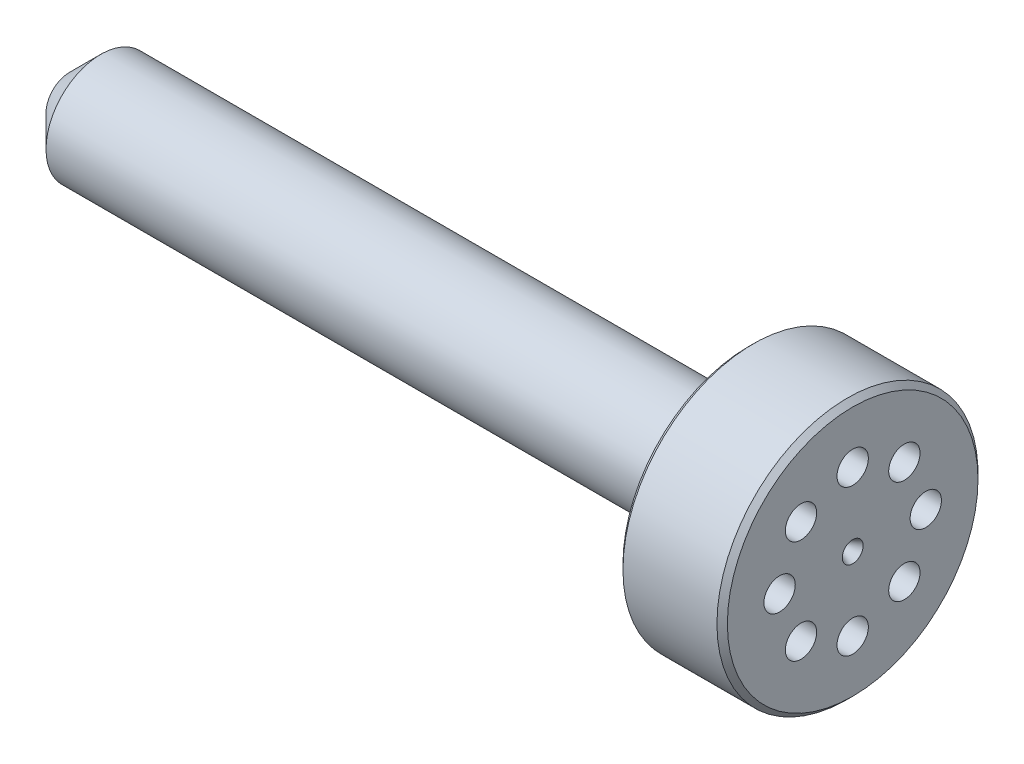
SolidWorks part; units mm, degrees
ref_plane "Front Plane" through (0, 0, 0) normal (0, 0, 1) x (1, 0, 0)
ref_plane "Top Plane" through (0, 0, 0) normal (0, 1, 0) x (1, 0, 0)
ref_plane "Right Plane" through (0, 0, 0) normal (1, 0, 0) x (0, 0, -1)
sketch "Sketch2" plane through (0, 0, 0) normal (0, 1, 0) x (1, 0, 0)
  line L0 (0, 0) -> (0, 17938.5923) construction
  line L1 (0, 0) -> (-17938.5923, 0) construction
  line L2 (-34, 1) -> (-34, 2.25)
  line L3 (-31, 5.25) -> (31, 5.25)
  line L4 (31, 5.25) -> (31, 12.5)
  line L5 (31, 12.5) -> (41, 12.5)
  line L6 (41, 12.5) -> (41, 1)
  line L7 (-34, 2.25) -> (-31, 5.25)
  line L8 (-32, 0) -> (39, 0)
  line L9 (-32, 0) -> (-34, 1)
  line L10 (41, 1) -> (39, 0)
  point P5 (-34, 0)
  point P6 (-34, 5.25)
  point P11 (41, 0)
  point P14 (0, 5.25)
  point P17 (0, 0)
  dimension "D1" = 5.25
  dimension "D2" = 65
  dimension "D3" = 12.5
  dimension "D4" = 10
  dimension "D5" = 1
  dimension "D6" = 2
  dimension "D7" = 32
  dimension "D10" = 1
  dimension "D11" = 2
  dimension "D12" = 8
revolve "Revolve1" add sketch "Sketch2" angle 360 about L8
chamfer "Chamfer1" distance 0.5 angle 45 2 edges at (41, 0, 12.5) (31, 0, 12.5)
sketch "Sketch3" plane through (41, 0, 0) normal (1, 0, 0) x (0, 0, -1)
  line L0 (0, 0) -> (0, 50000) construction
  line L1 (0, 0) -> (-50000, 0) construction
  circle A0 centre (0, 0) radius 7 construction
  circle A2 centre (0, 7) radius 1.5
  circle A3 centre (4.9497, 4.9497) radius 1.5
  circle A4 centre (7, 0) radius 1.5
  circle A5 centre (4.9497, -4.9497) radius 1.5
  circle A6 centre (0, -7) radius 1.5
  circle A7 centre (-4.9497, -4.9497) radius 1.5
  circle A8 centre (-7, 0) radius 1.5
  circle A9 centre (-4.9497, 4.9497) radius 1.5
  point P10 (0, 0)
  point P11 (0, 0)
  point P25 (0, 0)
  dimension "D1" = 14
  dimension "D2" = 3
  dimension "D3" = 8
extrude "Cut-Extrude1" cut sketch "Sketch3" against normal through all
